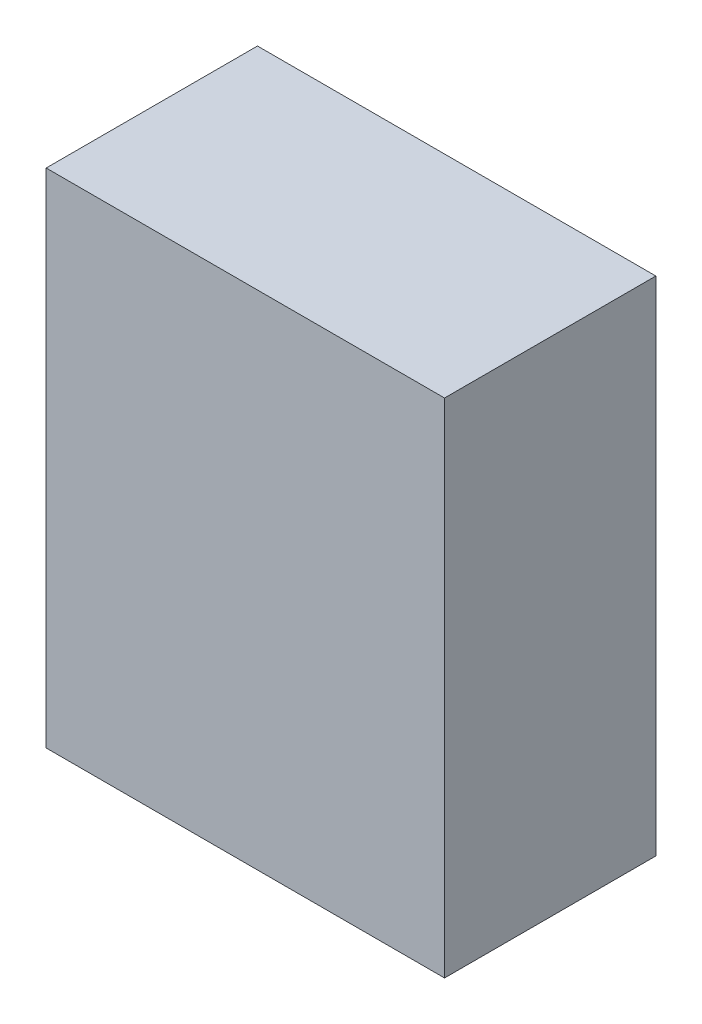
SolidWorks part; units mm, degrees
ref_plane "Front Plane" through (0, 0, 0) normal (0, 0, 1) x (1, 0, 0)
ref_plane "Top Plane" through (0, 0, 0) normal (0, 1, 0) x (1, 0, 0)
ref_plane "Right Plane" through (0, 0, 0) normal (1, 0, 0) x (0, 0, -1)
sketch "Sketch1" plane through (0, 0, 0) normal (0, 1, 0) x (1, 0, 0)
  line L1 (-8.7277, 6.4174) -> (14.2723, 6.4174)
  line L2 (-8.7277, 6.4174) -> (-8.7277, -5.7826)
  line L3 (-8.7277, -5.7826) -> (14.2723, -5.7826)
  line L4 (14.2723, 6.4174) -> (14.2723, -5.7826)
  dimension "D1" = 23
  dimension "D2" = 12.2
extrude "Boss-Extrude1" add sketch "Sketch1" along normal blind 29
